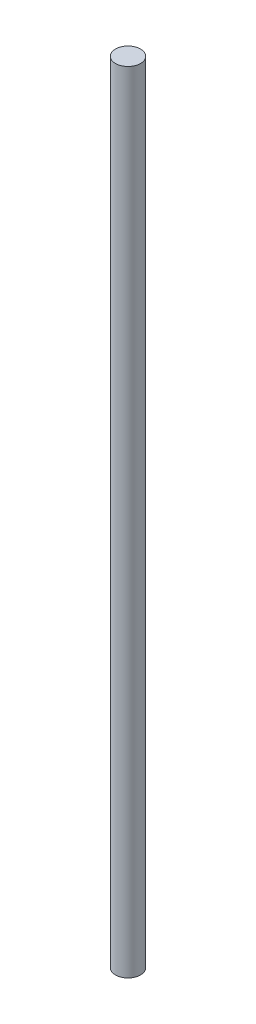
SolidWorks part; units mm, degrees
ref_plane "Front Plane" through (0, 0, 0) normal (0, 0, 1) x (1, 0, 0)
ref_plane "Top Plane" through (0, 0, 0) normal (0, 1, 0) x (1, 0, 0)
ref_plane "Right Plane" through (0, 0, 0) normal (1, 0, 0) x (0, 0, -1)
sketch "Sketch1" plane through (0, 0, 0) normal (0, 1, 0) x (1, 0, 0)
  circle A0 centre (0, 0) radius 3.175
  dimension "D1" = 6.35
extrude "Boss-Extrude1" add sketch "Sketch1" along normal blind 200
